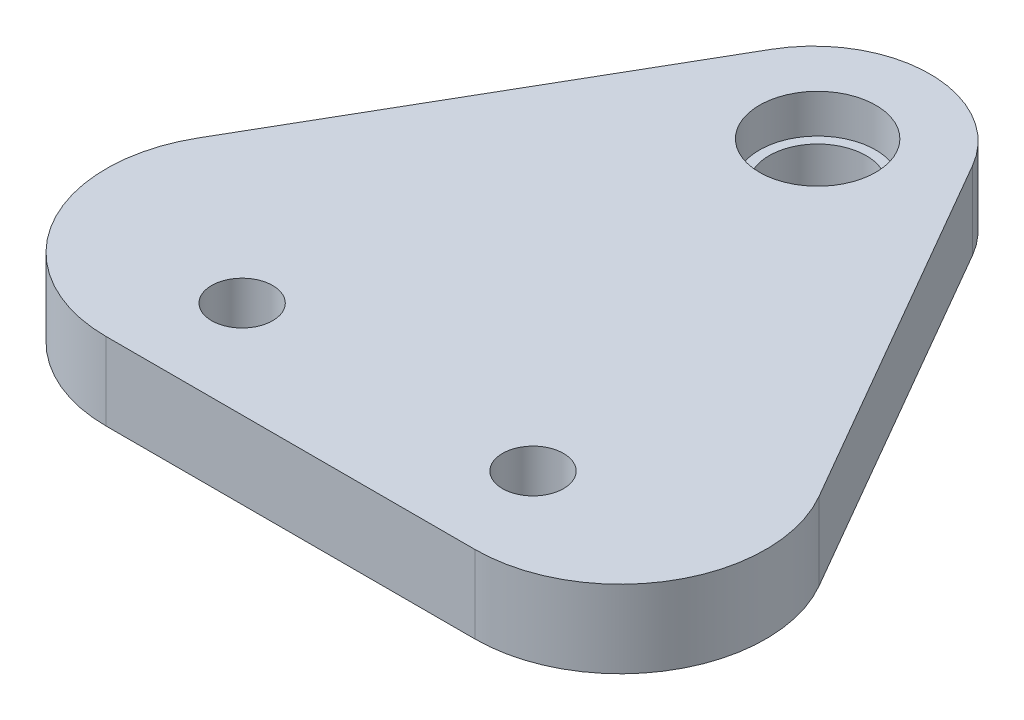
SolidWorks part; units mm, degrees
ref_plane "Front Plane" through (0, 0, 0) normal (0, 0, 1) x (1, 0, 0)
ref_plane "Top Plane" through (0, 0, 0) normal (0, 1, 0) x (1, 0, 0)
ref_plane "Right Plane" through (0, 0, 0) normal (1, 0, 0) x (0, 0, -1)
sketch "Sketch1" plane through (0, 0, 0) normal (0, 1, 0) x (1, 0, 0)
  line L3 (12.9904, 22.5) -> (34.6077, 59.9423)
  line L4 (25.9808, 0) -> (64.0192, 0)
  line L5 (77.0096, 22.5) -> (55.3923, 59.9423)
  arc A6 (64.0192, 0) -> (77.0096, 22.5) centre (64.0192, 15) ccw
  arc A7 (25.9808, 0) -> (12.9904, 22.5) centre (25.9808, 15) cw
  arc A8 (55.3923, 59.9423) -> (34.6077, 59.9423) centre (45, 53.9423) ccw
  point P8 (0, 0)
  point P11 (0, 0)
  dimension "D2" = 15
  dimension "D3" = 12
extrude "Boss-Extrude1" add sketch "Sketch1" along normal blind 8
sketch "Sketch2" plane through (0, 8, 0) normal (0, 1, 0) x (1, 0, 0)
  circle A2 centre (45, 54.3582) radius 6
  circle A5 centre (30, 10) radius 3
  circle A6 centre (60, 10) radius 3.15
  point P3 (57, 10)
  point P10 (57, 10)
extrude "Cut-Extrude1" cut sketch "Sketch2" against normal blind 4
sketch "Sketch3" plane through (0, 4, 0) normal (0, 1, 0) x (1, 0, 0)
  circle A0 centre (45, 54.3582) radius 5
extrude "Cut-Extrude2" cut sketch "Sketch3" against normal blind 10
sketch "Sketch4" plane through (0, 0, 0) normal (0, 1, 0) x (1, 0, 0)
  circle A0 centre (30, 10) radius 3.15
  circle A1 centre (60, 10) radius 3.15
extrude "Cut-Extrude4" cut sketch "Sketch4" along normal blind 11
sketch "Sketch5" plane through (0, 8, 0) normal (0, 1, 0) x (1, 0, 0)
  line L0 (60, 10) -> (45, 54.3582)
